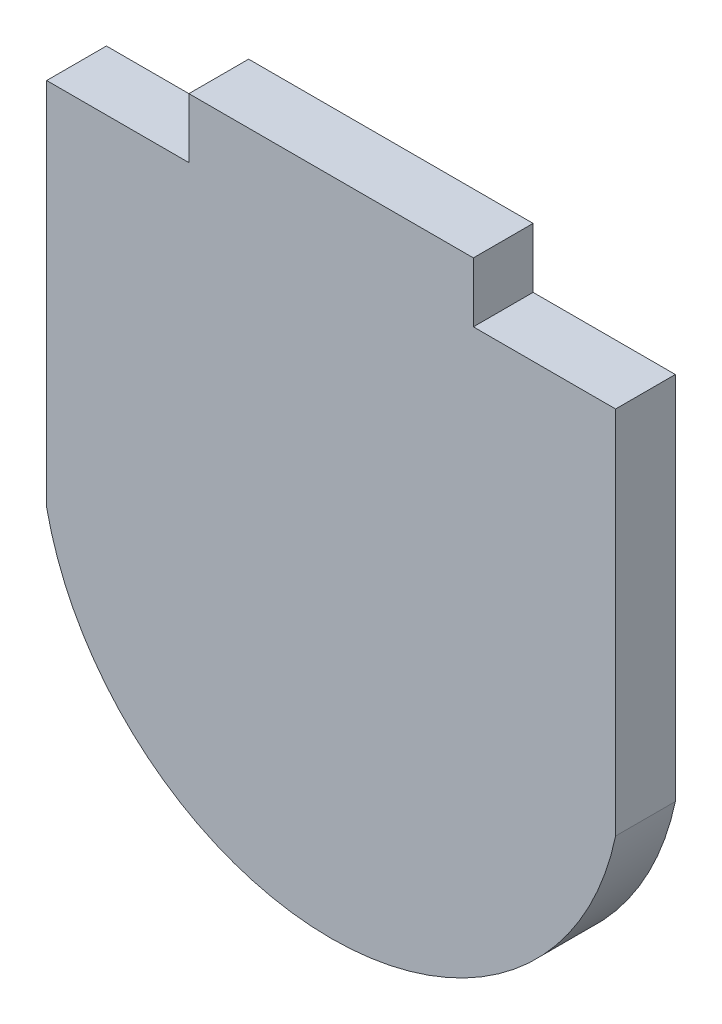
SolidWorks part; units mm, degrees
ref_plane "Front Plane" through (0, 0, 0) normal (0, 0, 1) x (1, 0, 0)
ref_plane "Top Plane" through (0, 0, 0) normal (0, 1, 0) x (1, 0, 0)
ref_plane "Right Plane" through (0, 0, 0) normal (1, 0, 0) x (0, 0, -1)
sketch "Sketch1" plane through (0, 0, 0) normal (0, 0, 1) x (1, 0, 0)
  line L0 (-38.121, 59.736) -> (-38.121, 98.09)
  line L1 (-38.121, 98.09) -> (12.679, 98.09)
  line L3 (-12.721, 98.09) -> (-12.721, -7.6778) construction
  line L4 (12.679, 98.09) -> (12.679, 59.736)
  arc A2 (-38.121, 59.736) -> (12.679, 59.736) centre (-12.721, 65.07) ccw
  dimension "D3" = 50.8
  dimension "D2" = 38.354
extrude "Boss-Extrude1" add sketch "Sketch1" along normal blind 5.334
sketch "Sketch2" plane through (0, 0, 5.334) normal (0, 0, 1) x (1, 0, 0)
  line L0 (-12.721, 98.09) -> (-12.721, 39.116) construction
  line L1 (-38.121, 98.09) -> (-25.421, 98.09)
  line L2 (-38.121, 98.09) -> (-38.121, 92.756)
  line L3 (-38.121, 92.756) -> (-25.421, 92.756)
  line L4 (-25.421, 98.09) -> (-25.421, 92.756)
  line L5 (12.679, 98.09) -> (-38.121, 98.09) construction
  line L6 (12.679, 92.756) -> (-0.021, 92.756)
  line L7 (-0.021, 98.09) -> (-0.021, 92.756)
  line L8 (12.679, 98.09) -> (-0.021, 98.09)
  line L9 (12.679, 98.09) -> (12.679, 92.756)
  arc A0 (-38.121, 59.736) -> (12.679, 59.736) centre (-12.721, 65.07) ccw construction
  dimension "D1" = 5.334
  dimension "D2" = 12.7
extrude "Cut-Extrude1" cut sketch "Sketch2" against normal through all
equation "\"GMaterial\" = 0.21in"
equation "\"MDF\"= 0.21in"
equation "\"Foamcore\"= 0.2in"
equation "\"D2@Sketch1\"=\"GMaterial\"+1.3"
equation "\"D1@Boss-Extrude1\"=\"GMaterial\""
equation "\"D1@Sketch2\"=\"GMaterial\""
